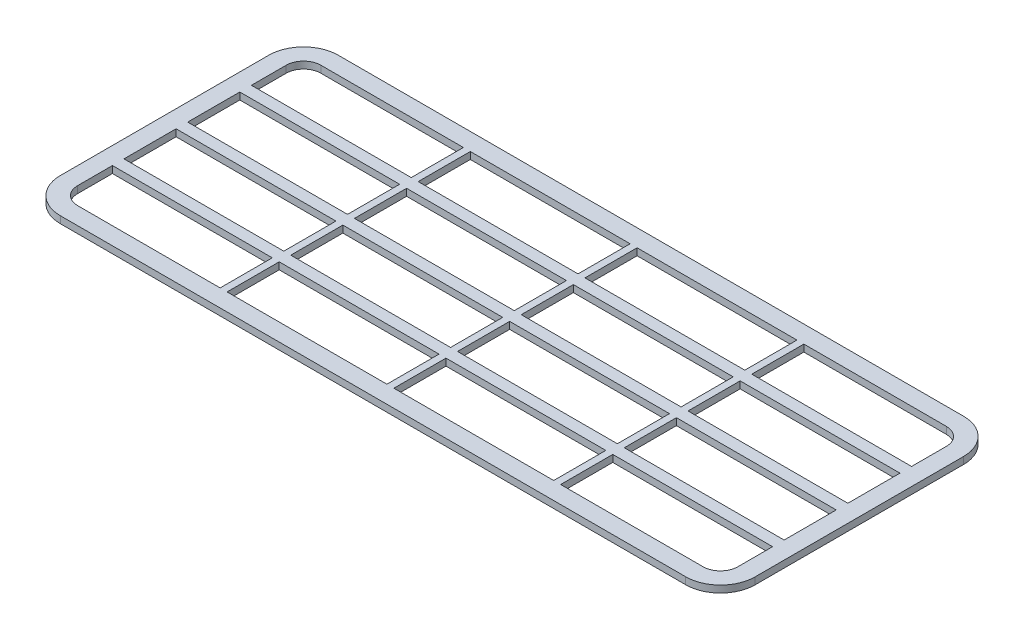
SolidWorks part; units mm, degrees
ref_plane "Front Plane" through (0, 0, 0) normal (0, 0, 1) x (1, 0, 0)
ref_plane "Top Plane" through (0, 0, 0) normal (0, 1, 0) x (1, 0, 0)
ref_plane "Right Plane" through (0, 0, 0) normal (1, 0, 0) x (0, 0, -1)
sketch "Sketch1" plane through (0, 0, 0) normal (0, 1, 0) x (1, 0, 0)
  line L0 (-71.1818, 16.8126) -> (-48.1818, 16.8126)
  line L1 (-68.6818, 26.8126) -> (21.3182, 26.8126)
  line L2 (-73.6818, 21.8126) -> (-73.6818, -8.1874)
  line L3 (-68.6818, -13.1874) -> (21.3182, -13.1874)
  line L4 (26.3182, 21.8126) -> (26.3182, -8.1874)
  line L5 (23.8182, 7.6426) -> (0.8182, 7.6426)
  line L6 (-71.1818, -3.1874) -> (-48.1818, -3.1874)
  line L7 (-47.1818, 24.3126) -> (-47.1818, 16.8126)
  line L8 (-23.1818, 24.3126) -> (-23.1818, 16.8126)
  line L9 (0.8182, 24.3126) -> (0.8182, 16.8126)
  line L10 (-48.1818, 24.3126) -> (-48.1818, 16.8126)
  line L11 (-68.6818, 24.3126) -> (-48.1818, 24.3126)
  line L12 (-71.1818, 21.8126) -> (-71.1818, 16.8126)
  line L13 (-68.6818, -10.6874) -> (-48.1818, -10.6874)
  line L14 (23.8182, 21.8126) -> (23.8182, 16.8126)
  line L15 (-24.1818, 24.3126) -> (-24.1818, 16.8126)
  line L16 (-0.1818, 24.3126) -> (-0.1818, 16.8126)
  line L17 (-47.1818, -10.6874) -> (-24.1818, -10.6874)
  line L18 (-47.1818, -3.1874) -> (-24.1818, -3.1874)
  line L19 (-48.1818, 7.6426) -> (-71.1818, 7.6426)
  line L20 (-47.1818, 16.8126) -> (-24.1818, 16.8126)
  line L21 (-47.1818, 24.3126) -> (-24.1818, 24.3126)
  line L22 (-23.1818, 24.3126) -> (-0.1818, 24.3126)
  line L23 (-23.1818, 16.8126) -> (-0.1818, 16.8126)
  line L24 (-24.1818, 7.6426) -> (-47.1818, 7.6426)
  line L25 (-23.1818, -3.1874) -> (-0.1818, -3.1874)
  line L26 (-23.1818, -10.6874) -> (-0.1818, -10.6874)
  line L27 (0.8182, -10.6874) -> (21.3182, -10.6874)
  line L28 (0.8182, -3.1874) -> (23.8182, -3.1874)
  line L29 (-0.1818, 7.6426) -> (-23.1818, 7.6426)
  line L30 (0.8182, 24.3126) -> (21.3182, 24.3126)
  line L31 (0.8182, 16.8126) -> (23.8182, 16.8126)
  line L32 (-71.1818, 15.1426) -> (-48.1818, 15.1426)
  line L33 (-71.1818, 5.9726) -> (-48.1818, 5.9726)
  line L34 (-71.1818, -1.5274) -> (-48.1818, -1.5274)
  line L35 (-71.1818, 15.1426) -> (-71.1818, 7.6426)
  line L36 (-48.1818, 15.1426) -> (-48.1818, 7.6426)
  line L37 (-47.1818, 15.1426) -> (-47.1818, 7.6426)
  line L38 (-47.1818, 15.1426) -> (-24.1818, 15.1426)
  line L39 (-71.1818, 5.9726) -> (-71.1818, -1.5274)
  line L40 (-48.1818, 5.9726) -> (-48.1818, -1.5274)
  line L41 (-47.1818, 5.9726) -> (-47.1818, -1.5274)
  line L42 (-47.1818, 5.9726) -> (-24.1818, 5.9726)
  line L43 (-71.1818, -3.1874) -> (-71.1818, -8.1874)
  line L44 (-48.1818, -3.1874) -> (-48.1818, -10.6874)
  line L45 (-47.1818, -3.1874) -> (-47.1818, -10.6874)
  line L46 (-47.1818, -1.5274) -> (-24.1818, -1.5274)
  line L47 (-24.1818, 15.1426) -> (-24.1818, 7.6426)
  line L48 (-23.1818, 15.1426) -> (-23.1818, 7.6426)
  line L49 (-23.1818, 15.1426) -> (-0.1818, 15.1426)
  line L50 (-24.1818, 5.9726) -> (-24.1818, -1.5274)
  line L51 (-23.1818, 5.9726) -> (-23.1818, -1.5274)
  line L52 (-23.1818, 5.9726) -> (-0.1818, 5.9726)
  line L53 (-24.1818, -3.1874) -> (-24.1818, -10.6874)
  line L54 (-23.1818, -3.1874) -> (-23.1818, -10.6874)
  line L55 (-23.1818, -1.5274) -> (-0.1818, -1.5274)
  line L56 (-0.1818, -3.1874) -> (-0.1818, -10.6874)
  line L57 (0.8182, -3.1874) -> (0.8182, -10.6874)
  line L58 (0.8182, -1.5274) -> (23.8182, -1.5274)
  line L59 (-0.1818, 5.9726) -> (-0.1818, -1.5274)
  line L60 (0.8182, 5.9726) -> (0.8182, -1.5274)
  line L61 (0.8182, 5.9726) -> (23.8182, 5.9726)
  line L62 (-0.1818, 15.1426) -> (-0.1818, 7.6426)
  line L63 (0.8182, 15.1426) -> (0.8182, 7.6426)
  line L64 (0.8182, 15.1426) -> (23.8182, 15.1426)
  line L65 (23.8182, 15.1426) -> (23.8182, 7.6426)
  line L66 (23.8182, 5.9726) -> (23.8182, -1.5274)
  line L67 (23.8182, -3.1874) -> (23.8182, -8.1874)
  line L68 (0.8182, -1.5274) -> (23.8182, -1.5274)
  arc A0 (21.3182, 26.8126) -> (26.3182, 21.8126) centre (21.3182, 21.8126) cw
  arc A1 (21.3182, -13.1874) -> (26.3182, -8.1874) centre (21.3182, -8.1874) ccw
  arc A2 (-73.6818, -8.1874) -> (-68.6818, -13.1874) centre (-68.6818, -8.1874) ccw
  arc A3 (-68.6818, 26.8126) -> (-73.6818, 21.8126) centre (-68.6818, 21.8126) ccw
  arc A4 (21.3182, -10.6874) -> (23.8182, -8.1874) centre (21.3182, -8.1874) ccw
  arc A5 (21.3182, 24.3126) -> (23.8182, 21.8126) centre (21.3182, 21.8126) cw
  arc A6 (-68.6818, 24.3126) -> (-71.1818, 21.8126) centre (-68.6818, 21.8126) ccw
  arc A7 (-71.1818, -8.1874) -> (-68.6818, -10.6874) centre (-68.6818, -8.1874) ccw
  dimension "D1" = 23
  dimension "D2" = 2.5
extrude "Boss-Extrude1" add sketch "Sketch1" along normal blind 1 contours L1 A3 L2 A2 L3 A1 L4 A0 A7 L43 L6 L44 L13 A6 L11 L10 L0 L12 A4 L27 L57 L28 L67 L61 L66 L58 L60 L64 L65 L5 L63 L49 L62 L29 L48 L52 L59 L55 L51 L25 L56 L26 L54
